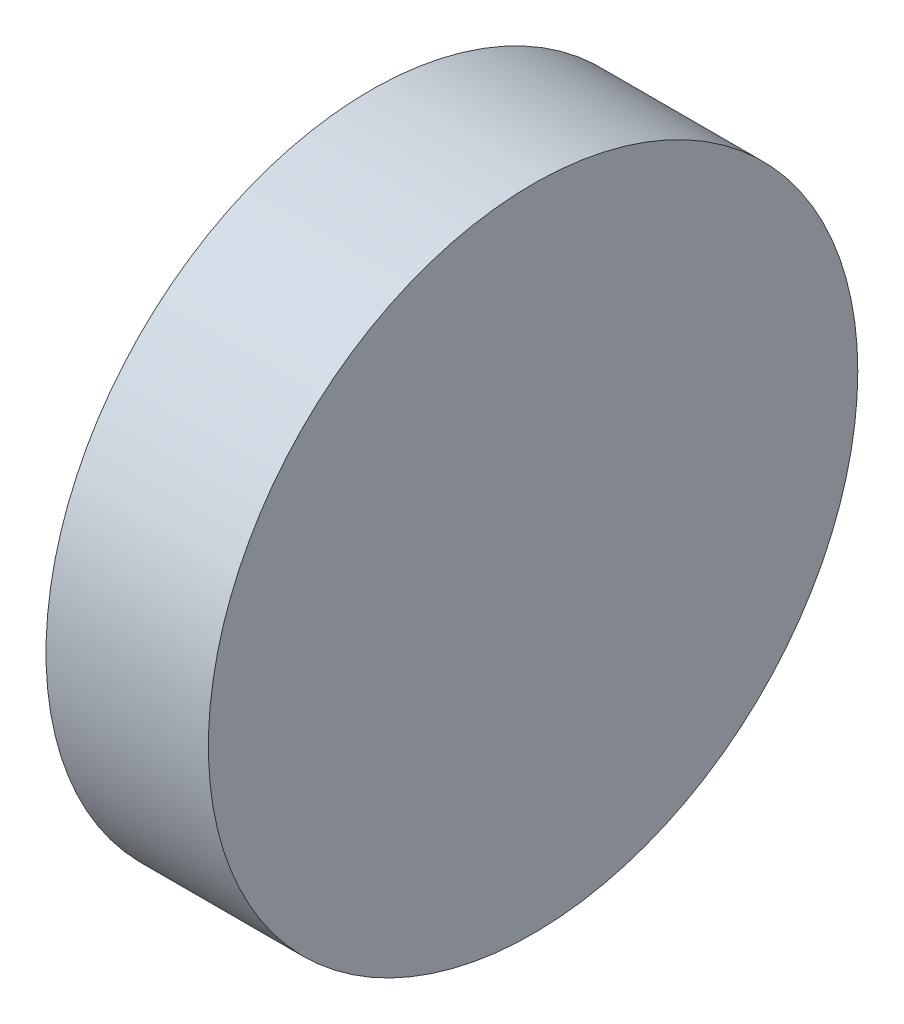
SolidWorks part; units mm, degrees
ref_plane "Front Plane" through (0, 0, 0) normal (0, 0, 1) x (1, 0, 0)
ref_plane "Top Plane" through (0, 0, 0) normal (0, 1, 0) x (1, 0, 0)
ref_plane "Right Plane" through (0, 0, 0) normal (1, 0, 0) x (0, 0, -1)
sketch "Sketch1" plane through (0, 0, 0) normal (1, 0, 0) x (0, 0, -1)
  circle A0 centre (0, 0) radius 152.4
  dimension "D1" = 304.8
extrude "Boss-Extrude1" add sketch "Sketch1" along normal blind 76.2
